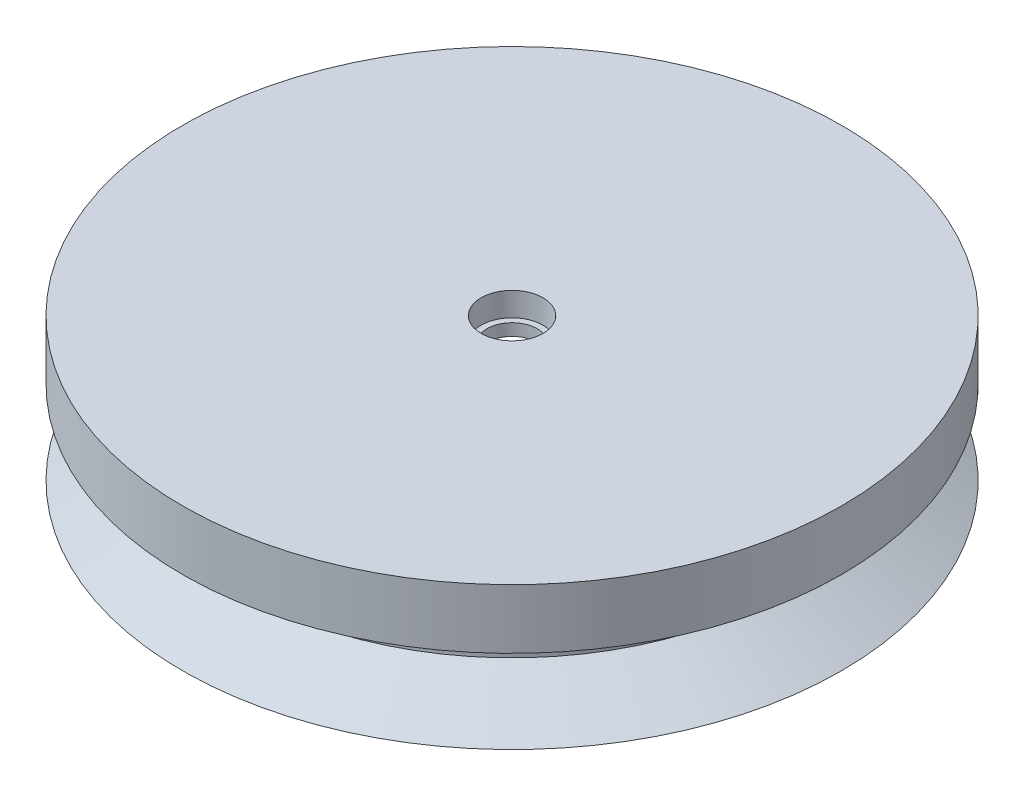
SolidWorks part; units mm, degrees
ref_plane "Front Plane" through (0, 0, 0) normal (0, 0, 1) x (1, 0, 0)
ref_plane "Top Plane" through (0, 0, 0) normal (0, 1, 0) x (1, 0, 0)
ref_plane "Right Plane" through (0, 0, 0) normal (1, 0, 0) x (0, 0, -1)
sketch "Sketch1" plane through (0, 0, 0) normal (0, 0, 1) x (1, 0, 0)
  line L0 (0, 0) -> (0, 7.7143) construction
  line L1 (2.1, 1) -> (2.6, 1)
  line L2 (2.6, 1) -> (2.6, 3)
  line L3 (2.6, 3) -> (27.6962, 3)
  line L5 (2.1, 0) -> (20, 0)
  line L6 (21, -2) -> (21, -9)
  line L7 (21, -9) -> (27.6962, -9)
  line L8 (27.6962, -9) -> (22.5, -6)
  line L9 (22.5, -5) -> (27.6962, -2)
  line L10 (27.6962, -2) -> (27.6962, 3)
  line L11 (21, -2) -> (20, -2)
  line L12 (20, -2) -> (20, 0)
  line L13 (22.5, -5) -> (22.5, -6)
  line L14 (2.1, 1) -> (2.1, 0)
  point P19 (22.5, -5.5)
  point P20 (21, -5.5)
  dimension "D1" = 42
  dimension "D2" = 7
  dimension "D3" = 1
  dimension "D4" = 2
  dimension "D5" = 5.2
  dimension "D6" = 2
  dimension "D7" = 0.5
  dimension "D8" = 45
  dimension "D9" = 1
  dimension "D10" = 1
  dimension "D11" = 30
revolve "Revolve1" add sketch "Sketch1" angle 360 about L0
equation "\"q\"=0.934754"
